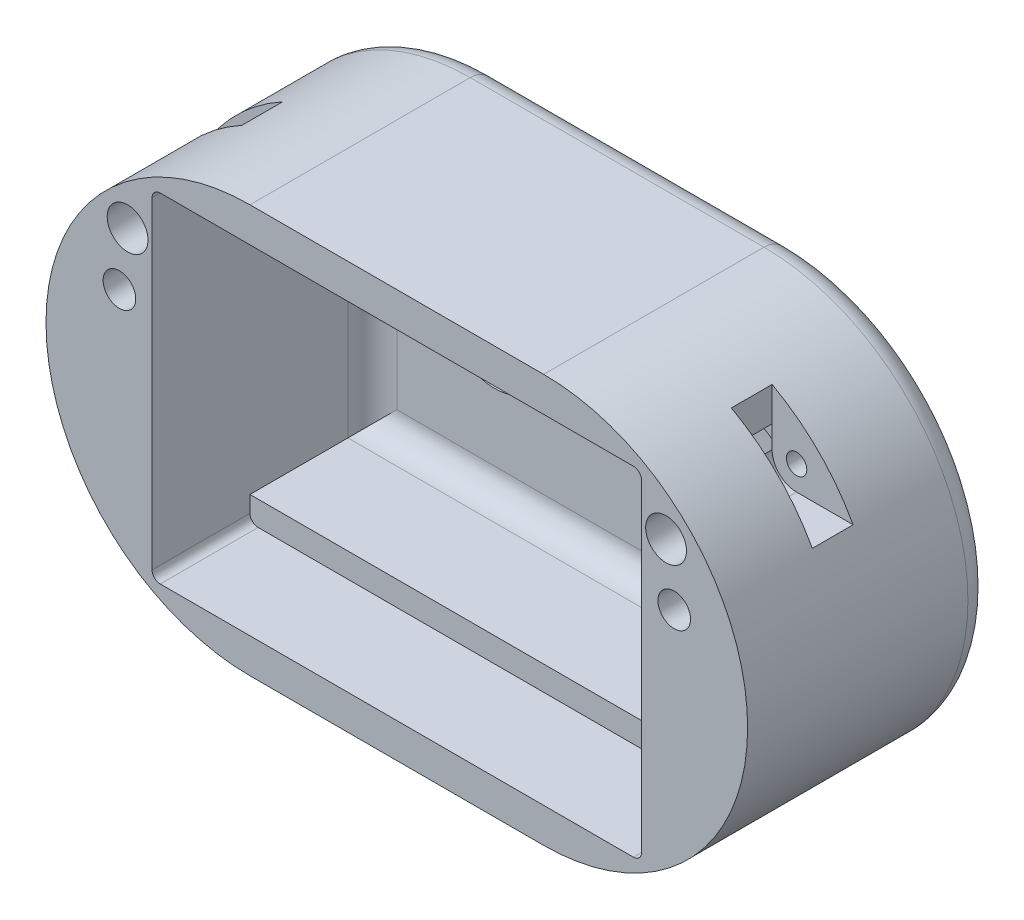
SolidWorks part; units mm, degrees
ref_plane "Front Plane" through (0, 0, 0) normal (0, 0, 1) x (1, 0, 0)
ref_plane "Top Plane" through (0, 0, 0) normal (0, 1, 0) x (1, 0, 0)
ref_plane "Right Plane" through (0, 0, 0) normal (1, 0, 0) x (0, 0, -1)
sketch "Sketch1" plane through (0, 0, 0) normal (0, 0, 1) x (1, 0, 0)
  line L0 (0, 0) -> (0, 45.304) construction
  line L1 (-18, 0) -> (18, 0) construction
  line L2 (-18, 25) -> (18, 25)
  line L3 (-18, -25) -> (18, -25)
  arc A0 (-18, 25) -> (-18, -25) centre (-18, 0) ccw
  arc A1 (18, -25) -> (18, 25) centre (18, 0) ccw
  point P4 (0, 0)
  dimension "D1" = 36
  dimension "D2" = 50
extrude "Boss-Extrude1" add sketch "Sketch1" along normal blind 30
sketch "Sketch2" plane through (0, 0, 30) normal (0, 0, 1) x (1, 0, 0)
  line L1 (-30, -20.75) -> (30, -20.75)
  line L2 (-30, -20.75) -> (-30, 20.75)
  line L3 (-30, 20.75) -> (30, 20.75)
  line L4 (30, -20.75) -> (30, 20.75)
  line L5 (-30, -20.75) -> (30, 20.75) construction
  line L6 (-30, 20.75) -> (30, -20.75) construction
  point P0 (0, 0)
  dimension "D1" = 41.5
  dimension "D2" = 60
extrude "Cut-Extrude1" cut sketch "Sketch2" against normal blind 27
sketch "Sketch3" plane through (0, 0, 0) normal (1, 0, 0) x (0, 0, -1)
  line L0 (0, 0) -> (-62.6932, 0) construction
sketch "Sketch5" plane through (0, 0, 3) normal (0, 0, 1) x (1, 0, 0)
  line L0 (30, -20.75) -> (30, 20.75) construction
  line L1 (-30, 20.75) -> (30, 20.75)
  line L2 (-30, 20.75) -> (-30, 17.75)
  line L3 (-30, 17.75) -> (30, 17.75)
  line L4 (30, 20.75) -> (30, 17.75)
  line L5 (-30, 20.75) -> (-30, -20.75) construction
  line L6 (30, -20.75) -> (-30, -20.75)
  line L7 (30, -20.75) -> (30, -17.75)
  line L8 (30, -17.75) -> (-30, -17.75)
  line L9 (-30, -20.75) -> (-30, -17.75)
  dimension "D1" = 3
  dimension "D2" = 3
extrude "Boss-Extrude2" add sketch "Sketch5" along normal blind 15
fillet "Fillet2" radius 1 4 edges at (-30, -20.75, 24) (30, -20.75, 24) (30, 20.75, 24) (-30, 20.75, 24)
fillet "Fillet3" radius 3 4 edges at (30, 0, 3) (0, -17.75, 3) (-30, 0, 3) (0, 17.75, 3)
fillet "Fillet4" radius 3 4 edges at (0, 25, 0) (43, 0, 0) (0, -25, 0) (-43, 0, 0)
sketch "Sketch6" plane through (0, 0, 0) normal (0, 0, 1) x (1, 0, 0)
  line L0 (-44.2964, 12) -> (-33, 12)
  line L1 (-30, 15) -> (-30, 24.1042)
  line L2 (-30, 24.1042) -> (-44.2964, 12)
  line L3 (0, 0) -> (0, 31.0101) construction
  line L4 (30, 24.1042) -> (44.2964, 12)
  line L5 (30, 15) -> (30, 24.1042)
  line L6 (44.2964, 12) -> (33, 12)
  arc A0 (-33, 12) -> (-30, 15) centre (-33, 15) ccw
  arc A1 (33, 12) -> (30, 15) centre (33, 15) cw
  dimension "D3" = 3
  dimension "D1" = 30
  dimension "D2" = 12
extrude "Cut-Extrude2" cut sketch "Sketch6" along normal blind 5 from offset 14
sketch "Sketch7" plane through (0, 0, 0) normal (0, 0, -1) x (-1, 0, 0)
  circle A0 centre (-33, 15) radius 1.25
  dimension "D1" = 2.5
  dimension "D2" = 33
  dimension "D3" = 15
extrude "Cut-Extrude3" cut sketch "Sketch7" along normal blind 25 from surface at -30 starting at face at (0, 0, 30)
sketch "Sketch8" plane through (0, 0, 30) normal (0, 0, 1) x (1, 0, 0)
  circle A0 centre (33, 15) radius 2.5
  dimension "D1" = 5
extrude "Cut-Extrude4" cut sketch "Sketch8" against normal blind 4
mirror "Mirror1" about plane through (0, 0, 0) normal (1, 0, 0) of "Cut-Extrude4", "Cut-Extrude3"
sketch "Sketch9" plane through (0, 0, 3) normal (0, 0, 1) x (1, 0, 0)
  line L0 (-15, 0) -> (15, 0) construction
  circle A0 centre (-15, 0) radius 6.5
  circle A1 centre (15, 0) radius 6.5
  dimension "D1" = 13
  dimension "D2" = 30
extrude "Cut-Extrude5" cut sketch "Sketch9" against normal blind 1.75
sketch "Sketch10" plane through (0, 0, 0) normal (0, 0, -1) x (-1, 0, 0)
  line L0 (0, 0) -> (0, 33.227) construction
  circle A0 centre (-34, 8) radius 2
  circle A1 centre (34, 8) radius 2
  dimension "D1" = 4
  dimension "D2" = 8
  dimension "D3" = 34
extrude "Cut-Extrude6" cut sketch "Sketch10" against normal through all
sketch "Sketch11" plane through (0, 0, 0) normal (0, 0, -1) x (-1, 0, 0)
  circle A0 centre (-34, 8) radius 3.5
  circle A1 centre (34, 8) radius 3.5
  dimension "D1" = 7
  dimension "D2" = 7
extrude "Cut-Extrude7" cut sketch "Sketch11" against normal blind 10
